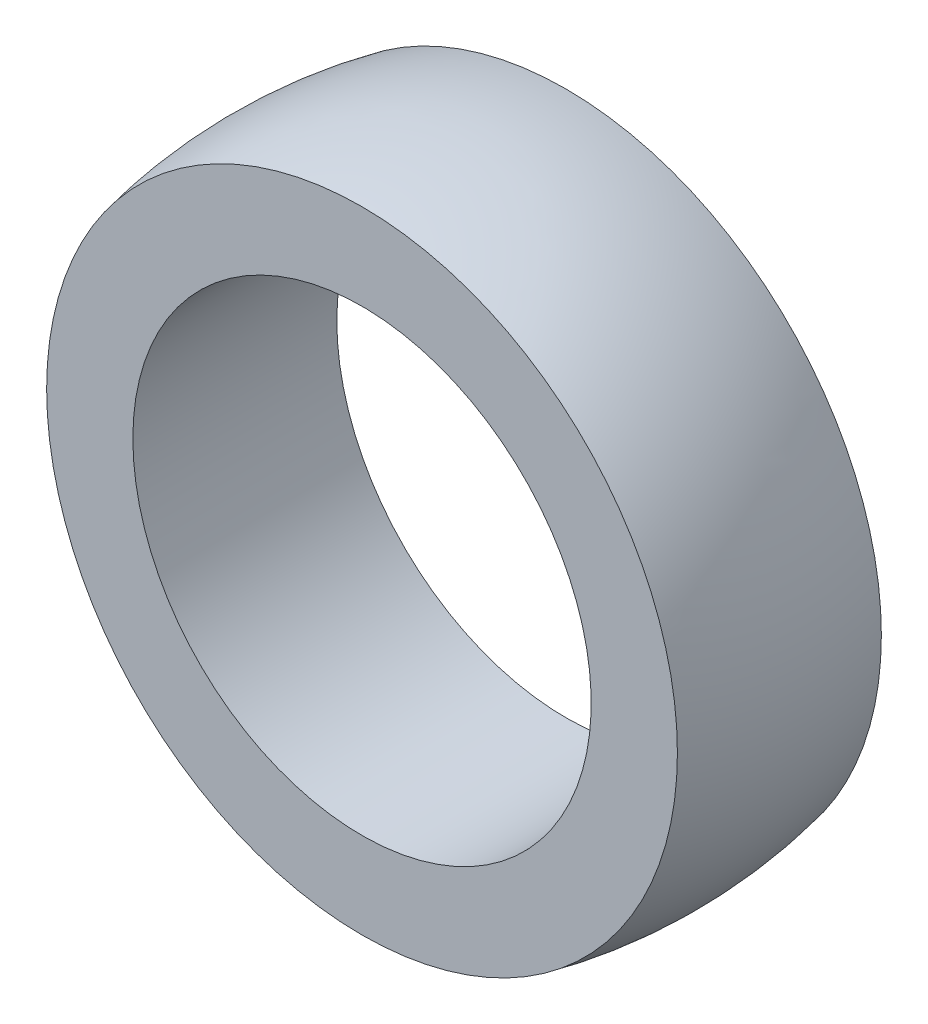
SolidWorks part; units mm, degrees
material "Silicon Rubber"
ref_plane "Front Plane" through (0, 0, 0) normal (0, 0, 1) x (1, 0, 0)
ref_plane "Top Plane" through (0, 0, 0) normal (0, 1, 0) x (1, 0, 0)
ref_plane "Right Plane" through (0, 0, 0) normal (1, 0, 0) x (0, 0, -1)
sketch "Sketch2" plane through (0, 0, 0) normal (1, 0, 0) x (0, 0, -1)
  line L2 (-12.319, 38.1) -> (-12.319, 27.686)
  line L3 (-12.319, 27.686) -> (12.319, 27.686)
  line L4 (12.319, 38.1) -> (12.319, 27.686)
  arc A2 (-12.319, 38.1) -> (12.319, 38.1) centre (0, -21.0122) cw
  point P4 (0, 27.686)
  point P7 (0, 0)
  point P8 (0, 0)
  point P9 (0, 13.0612)
  point P10 (0, 39.37)
  dimension "D2" = 24.638
  dimension "D3" = 27.686
  dimension "D4" = 1.27
  dimension "D1" = 10.414
ref_axis "Axis1" through (0, 0, 0) along (0, 0, 1)
revolve "Revolve1" add sketch "Sketch2" angle 360 about axis through (0, 0, 0) along (0, 0, 1)
